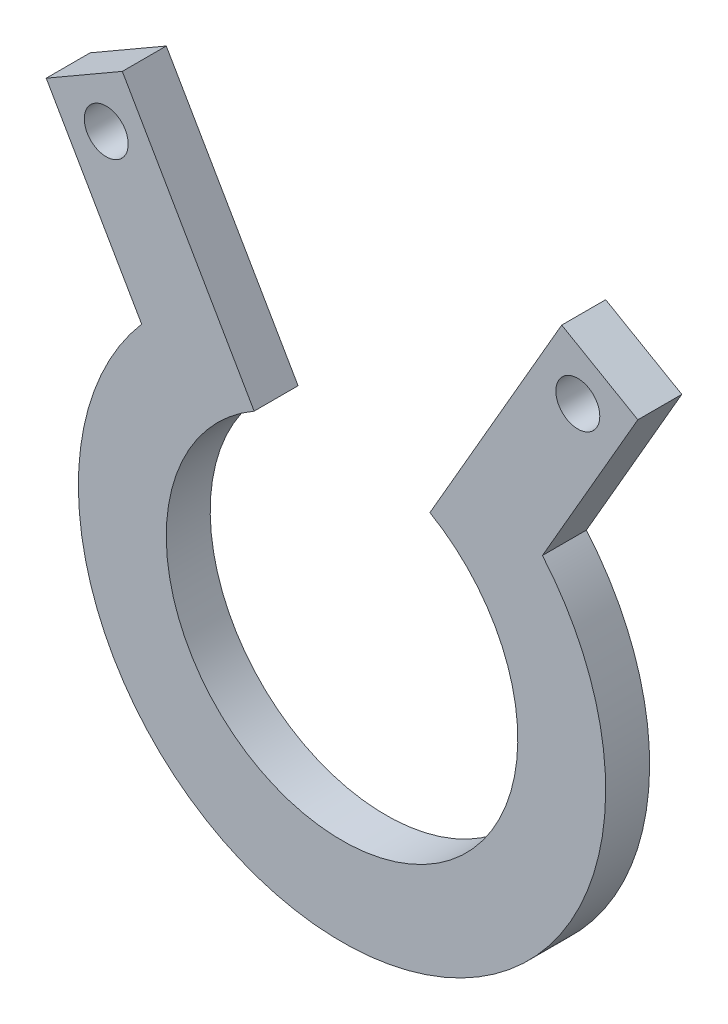
SolidWorks part; units mm, degrees
ref_plane "Front Plane" through (0, 0, 0) normal (0, 0, 1) x (1, 0, 0)
ref_plane "Top Plane" through (0, 0, 0) normal (0, 1, 0) x (1, 0, 0)
ref_plane "Right Plane" through (0, 0, 0) normal (1, 0, 0) x (0, 0, -1)
sketch "Sketch2" plane through (0, 0, 0) normal (0, 0, 1) x (1, 0, 0)
  circle A0 centre (0, 0) radius 15.875
  circle A1 centre (0, 0) radius 19.05
  circle A2 centre (0, 0) radius 12.7
  dimension "D1" = 31.75
  dimension "D2" = 3.175
  dimension "D3" = 3.175
extrude "Boss-Extrude1" add sketch "Sketch2" along normal blind 3.175 contours A1 A0 | A0 A2
sketch "Sketch3" plane through (0, 0, 3.175) normal (0, 0, 1) x (1, 0, 0)
  line L0 (-18.6246, 25.9088) -> (-17.0371, 23.1592) construction
  line L1 (0, 0) -> (-9.525, 16.4978) construction
  line L2 (0, 0) -> (0, 19.05) construction
  line L3 (-9.525, 16.4978) -> (-15.875, 27.4963)
  line L4 (-15.875, 27.4963) -> (-21.3743, 24.3213)
  line L5 (-21.3743, 24.3213) -> (-14.4795, 12.3793)
  line L6 (-15.875, 27.4963) -> (-8.9803, 15.5543)
  line L7 (-15.0243, 13.3228) -> (-21.3743, 24.3213)
  line L8 (18.6246, 25.9088) -> (17.0371, 23.1592) construction
  line L9 (15.0243, 13.3228) -> (21.3743, 24.3213)
  line L10 (15.875, 27.4963) -> (8.9803, 15.5543)
  line L11 (21.3743, 24.3213) -> (14.4795, 12.3793)
  line L12 (15.875, 27.4963) -> (21.3743, 24.3213)
  line L13 (9.525, 16.4978) -> (15.875, 27.4963)
  circle A0 centre (0, 0) radius 19.05 construction
  circle A2 centre (-17.0371, 23.1592) radius 1.5875
  circle A3 centre (17.0371, 23.1592) radius 1.5875
  circle M7 centre (0, 0) radius 19.05
  dimension "D5" = 3.175
  dimension "D1" = 30
  dimension "D2" = 3.175
  dimension "D3" = 12.7
  dimension "D4" = 6.35
extrude "Boss-Extrude2" add sketch "Sketch3" against normal up to surface (3.175 mm away) contours L4 L5 L3 A2 M7 | L12 L10 L11 L9 A3 M7 up to face at (19.05, 0, 0)
ref_plane "Plane4" through (-15.875, 27.4963, 3.175) normal (0, 0, 1) x (1, 0, 0)
sketch "Sketch5" plane through (0, 0, 3.175) normal (0, 0, 1) x (1, 0, 0)
  line L0 (-9.525, 16.4978) -> (0, 0)
  line L1 (0, 0) -> (9.525, 16.4978)
  arc A0 (9.525, 16.4978) -> (-9.525, 16.4978) centre (0, 0) ccw construction
  arc A1 (9.525, 16.4978) -> (-9.525, 16.4978) centre (0, 0) ccw
extrude "Cut-Extrude1" cut sketch "Sketch5" against normal up to surface (3.175 mm away) up to face at (0, 16.564, 0)
